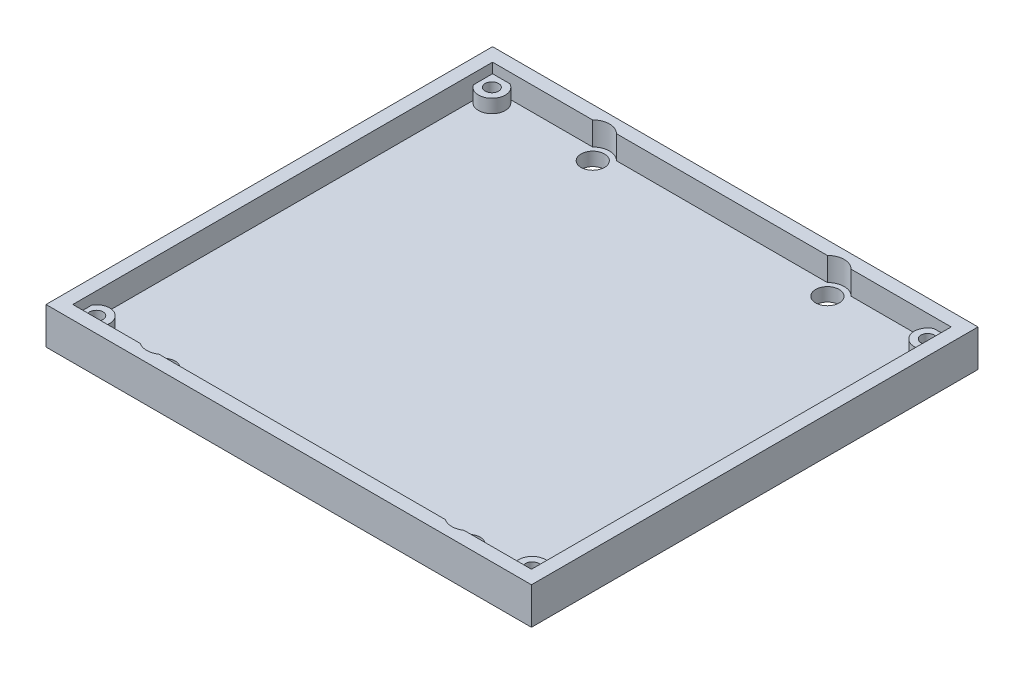
SolidWorks part; units mm, degrees
ref_plane "Front Plane" through (0, 0, 0) normal (0, 0, 1) x (1, 0, 0)
ref_plane "Top Plane" through (0, 0, 0) normal (0, 1, 0) x (1, 0, 0)
ref_plane "Right Plane" through (0, 0, 0) normal (1, 0, 0) x (0, 0, -1)
sketch "Sketch1" plane through (0, 0, 0) normal (0, 1, 0) x (1, 0, 0)
  line L0 (18.7, 62.8437) -> (36.2, 62.8437) construction
  line L7 (18.7, 62.8437) -> (13.45, 4.0777) construction
  line L8 (36.2, 62.8437) -> (36.2, 4.0777) construction
  line L9 (13.45, 4.0777) -> (36.2, 4.0777) construction
  line L10 (18.7, 62.8437) -> (18.7, 4.0777) construction
  line L11 (36.2, 33.4607) -> (0, 33.3) construction
  line L12 (0, 0) -> (72.4, 0)
  line L13 (0, 0) -> (0, 66.6)
  line L14 (0, 66.6) -> (72.4, 66.6)
  line L15 (72.4, 0) -> (72.4, 66.6)
  line L16 (36.2, 33.4607) -> (72.4, 33.3) construction
  circle A0 centre (18.7, 62.8437) radius 1.75
  circle A4 centre (13.45, 4.0777) radius 1.75
  circle A5 centre (58.95, 4.0777) radius 1.75
  circle A6 centre (53.7, 62.8437) radius 1.75
  dimension "D1" = 3.5
  dimension "D2" = 17.5
  dimension "D3" = 59
  dimension "D4" = 22.75
  dimension "D5" = 72.4
  dimension "D6" = 66.6
extrude "Boss-Extrude1" add sketch "Sketch1" along normal blind 2
sketch "Sketch2" plane through (0, 2, 0) normal (0, 1, 0) x (1, 0, 0)
  line L0 (3.7, 3.8) -> (3.7, 0) construction
  line L1 (0, 0) -> (72.4, 0) construction
  line L2 (3.7, 62.8) -> (3.7, 66.6) construction
  line L3 (72.4, 66.6) -> (0, 66.6) construction
  line L4 (3.7, 3.8) -> (0, 3.8) construction
  line L5 (0, 66.6) -> (0, 0) construction
  line L6 (68.7, 3.8) -> (72.4, 3.8) construction
  line L7 (72.4, 0) -> (72.4, 66.6) construction
  line L8 (36.2, 66.6) -> (36.2, 0) construction
  line L9 (0, 66.6) -> (72.4, 66.6)
  line L10 (0, 66.6) -> (0, 0)
  line L11 (3.7, 2) -> (12.0596, 2)
  line L12 (2, 3.8) -> (2, 61.7464)
  line L13 (3.7, 64.6) -> (16.9209, 64.6)
  line L14 (70.4, 3.8) -> (70.4, 61.7464)
  line L15 (0, 0) -> (72.4, 0)
  line L16 (72.4, 66.6) -> (72.4, 0)
  line L17 (0, 33.3) -> (72.4, 33.3) construction
  line L18 (14.8404, 2) -> (57.5596, 2)
  line L19 (60.3404, 2) -> (67.8282, 2)
  line L20 (18.7, 62.8437) -> (20.45, 62.8437) construction
  line L21 (20.4791, 64.6) -> (51.9209, 64.6)
  line L22 (55.4791, 64.6) -> (67.8282, 64.6)
  circle A0 centre (3.7, 3.8) radius 1
  circle A1 centre (68.7, 3.8) radius 1
  circle A2 centre (68.7, 62.8) radius 1
  circle A3 centre (3.7, 62.8) radius 1
  arc A4 (4.5718, 64.6) -> (2, 61.7464) centre (3.7, 62.8) cw
  arc A5 (4.5718, 2) -> (2, 4.8536) centre (3.7, 3.8) ccw
  arc A6 (67.8282, 2) -> (70.4, 4.8536) centre (68.7, 3.8) cw
  arc A7 (67.8282, 64.6) -> (70.4, 61.7464) centre (68.7, 62.8) ccw
  arc A8 (12.0596, 2) -> (14.8404, 2) centre (13.45, 4.0777) ccw
  arc A9 (60.3404, 2) -> (57.5596, 2) centre (58.95, 4.0777) cw
  circle A10 centre (18.7, 62.8437) radius 1.75 construction
  arc A11 (20.4791, 64.6) -> (16.9209, 64.6) centre (18.7, 62.8437) ccw
  arc A12 (51.9209, 64.6) -> (55.4791, 64.6) centre (53.7, 62.8437) cw
  line M7 (0, 66.6) -> (0, 0)
  line M8 (0, 0) -> (72.4, 0)
  line M9 (72.4, 0) -> (72.4, 66.6)
  line M10 (72.4, 66.6) -> (0, 66.6)
  dimension "D1" = 2
  dimension "D8" = 1
  dimension "D6" = 2.5
  dimension "D7" = 2.5
  dimension "D2" = 2
  dimension "D3" = 2
  dimension "D4" = 2
  dimension "D5" = 2
extrude "Boss-Extrude2" add sketch "Sketch2" along normal blind 2 contours L14 L11 L12 L13 M10 M7 M8 M9
sketch "Sketch3" plane through (0, 4, 0) normal (0, 1, 0) x (1, 0, 0)
  line L0 (2, 61.7464) -> (2, 64.6) construction
  line L1 (4.5718, 64.6) -> (2, 64.6) construction
  line L2 (67.8282, 2) -> (70.4, 2) construction
  line L3 (70.4, 4.8536) -> (70.4, 2) construction
  line L4 (12.0596, 2) -> (2, 2)
  line L5 (70.4, 2) -> (60.3404, 2)
  line L6 (70.4, 2) -> (70.4, 64.6)
  line L7 (70.4, 64.6) -> (55.4791, 64.6)
  line L8 (2, 2) -> (2, 64.6)
  line L9 (0, 66.6) -> (72.4, 66.6)
  line L10 (0, 66.6) -> (0, 0)
  line L11 (0, 0) -> (72.4, 0)
  line L12 (72.4, 66.6) -> (72.4, 0)
  line L13 (57.5596, 2) -> (14.8404, 2)
  line L14 (16.9209, 64.6) -> (2, 64.6)
  line L15 (51.9209, 64.6) -> (20.4791, 64.6)
  arc A0 (12.0596, 2) -> (14.8404, 2) centre (13.45, 4.0777) ccw
  arc A1 (12.0596, 2) -> (14.8404, 2) centre (13.45, 4.0777) ccw construction
  arc A2 (60.3404, 2) -> (57.5596, 2) centre (58.95, 4.0777) cw
  arc A3 (16.9209, 64.6) -> (20.4791, 64.6) centre (18.7, 62.8437) cw
  arc A4 (51.9209, 64.6) -> (55.4791, 64.6) centre (53.7, 62.8437) cw
extrude "Boss-Extrude3" add sketch "Sketch3" along normal blind 1.5
